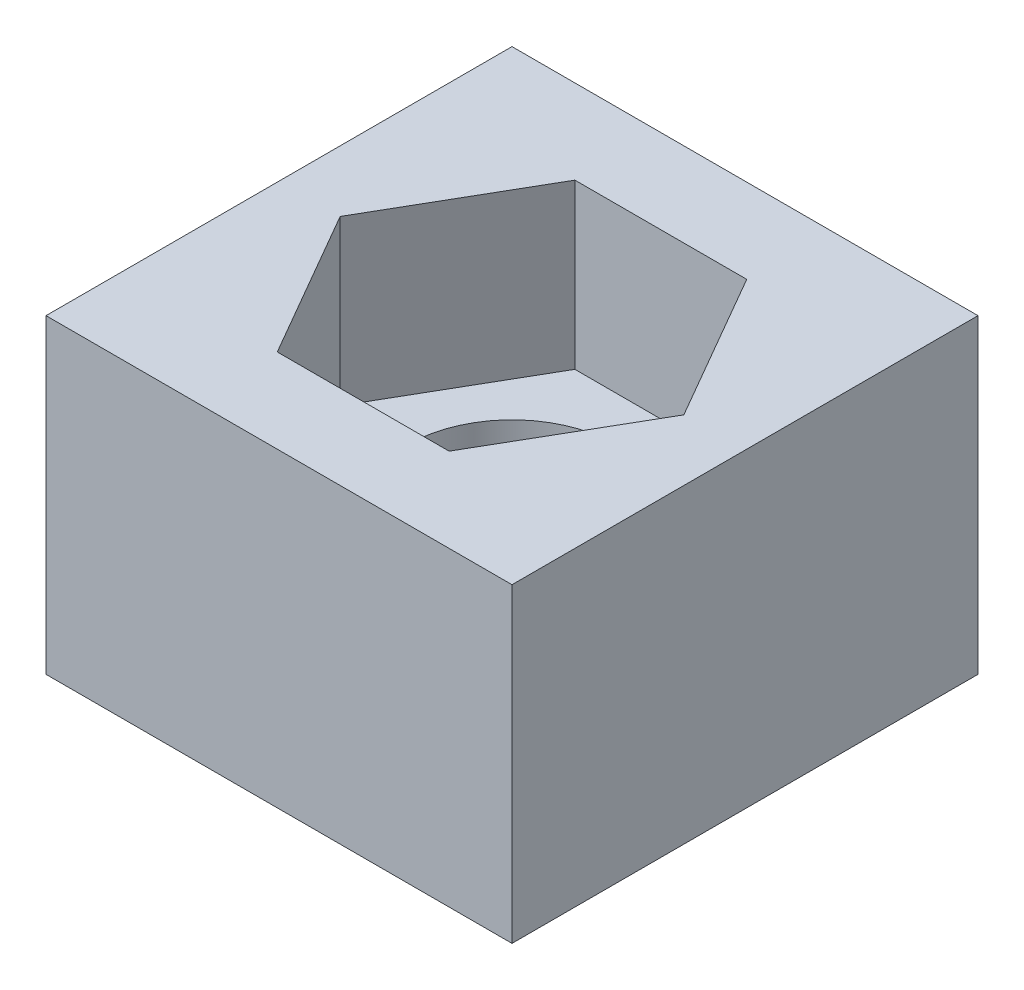
SolidWorks part; units mm, degrees
ref_plane "Front Plane" through (0, 0, 0) normal (0, 0, 1) x (1, 0, 0)
ref_plane "Top Plane" through (0, 0, 0) normal (0, 1, 0) x (1, 0, 0)
ref_plane "Right Plane" through (0, 0, 0) normal (1, 0, 0) x (0, 0, -1)
sketch "Sketch1" plane through (0, 0, 0) normal (0, 1, 0) x (1, 0, 0)
  line L1 (0, 0) -> (38.1018, 0)
  line L2 (0, 0) -> (0, 38.1018)
  line L3 (0, 38.1018) -> (38.1018, 38.1018)
  line L4 (38.1018, 0) -> (38.1018, 38.1018)
extrude "Boss-Extrude1" add sketch "Sketch1" along normal blind 25.4
sketch "Sketch2" plane through (0, 25.4, 0) normal (0, 1, 0) x (1, 0, 0)
  line L1 (33.1009, 19.0509) -> (26.0759, 31.2186)
  line L2 (26.0759, 31.2186) -> (12.0259, 31.2186)
  line L3 (12.0259, 31.2186) -> (5.0009, 19.0509)
  line L4 (5.0009, 19.0509) -> (12.0259, 6.8833)
  line L5 (12.0259, 6.8833) -> (26.0759, 6.8833)
  line L6 (26.0759, 6.8833) -> (33.1009, 19.0509)
  circle A0 centre (19.0509, 19.0509) radius 12.1677 construction
extrude "Cut-Extrude1" cut sketch "Sketch2" against normal blind 13.4
sketch "Sketch4" plane through (0, 0, 0) normal (0, -1, 0) x (1, 0, 0)
  circle A0 centre (19.0509, -19.0509) radius 8.523
extrude "Cut-Extrude2" cut sketch "Sketch4" against normal up to surface (12 mm away) up to face at (19.0509, 12, -19.0509)
